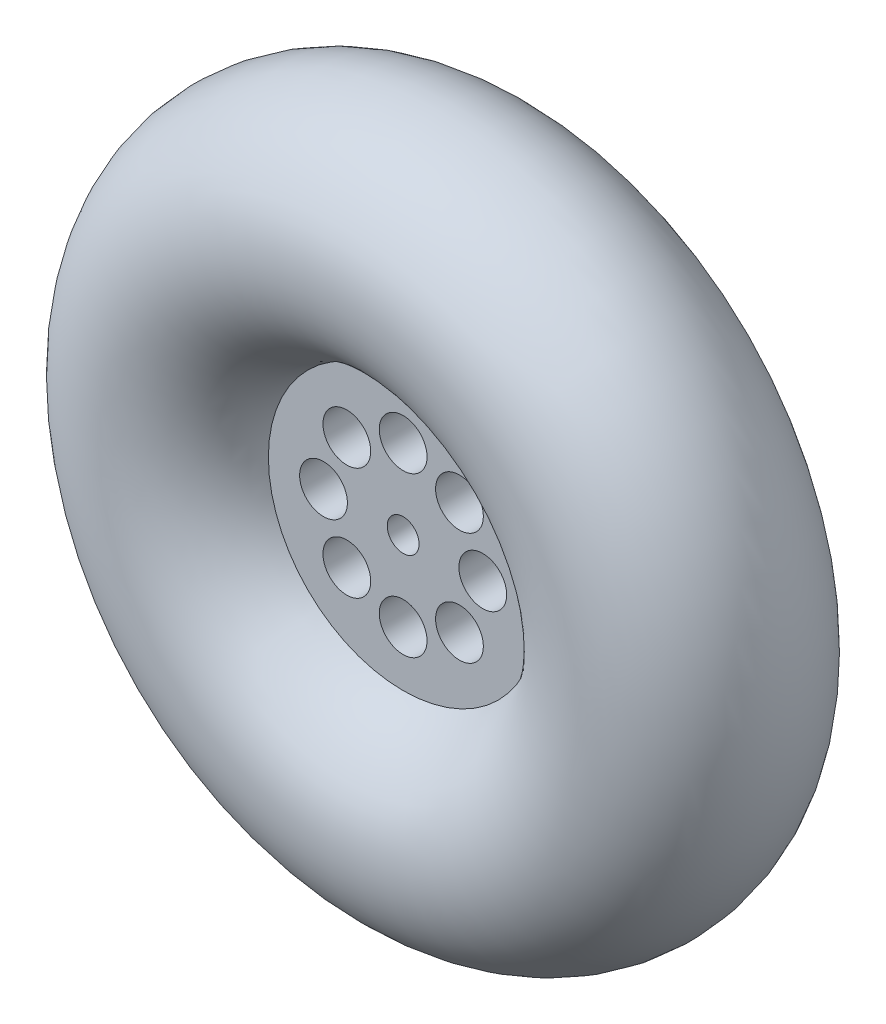
SolidWorks part; units mm, degrees
ref_plane "前视基准面" through (0, 0, 0) normal (0, 0, 1) x (1, 0, 0)
ref_plane "上视基准面" through (0, 0, 0) normal (0, 1, 0) x (1, 0, 0)
ref_plane "右视基准面" through (0, 0, 0) normal (1, 0, 0) x (0, 0, -1)
sketch "草图1" plane through (0, 0, 0) normal (1, 0, 0) x (0, 0, -1)
  circle A0 centre (0, 30) radius 14
  point P2 (0, 0)
ref_axis "基准轴1" through (0, 0, 15.4) along (0, 0, -1)
revolve "旋转1" add sketch "草图1" angle 360 about axis through (0, 0, 15.4) along (0, 0, -1)
sketch "草图2" plane through (0, 0, 0) normal (0, 0, 1) x (1, 0, 0)
  circle A0 centre (0, 0) radius 18
  circle A1 centre (0, 0) radius 2
extrude "凸台-拉伸2" add sketch "草图2" along normal mid plane 10 separate body
sketch "草图3" plane through (0, 0, 5) normal (0, 0, 1) x (1, 0, 0)
  circle A0 centre (0, 10) radius 3
  circle A1 centre (7.0711, 7.0711) radius 3
  circle A2 centre (10, 0) radius 3
  circle A3 centre (7.0711, -7.0711) radius 3
  circle A4 centre (0, -10) radius 3
  circle A5 centre (-7.0711, -7.0711) radius 3
  circle A6 centre (-10, 0) radius 3
  circle A7 centre (-7.0711, 7.0711) radius 3
  point P18 (0, 0)
  dimension "D1" = 8
extrude "切除-拉伸1" cut sketch "草图3" against normal through all
